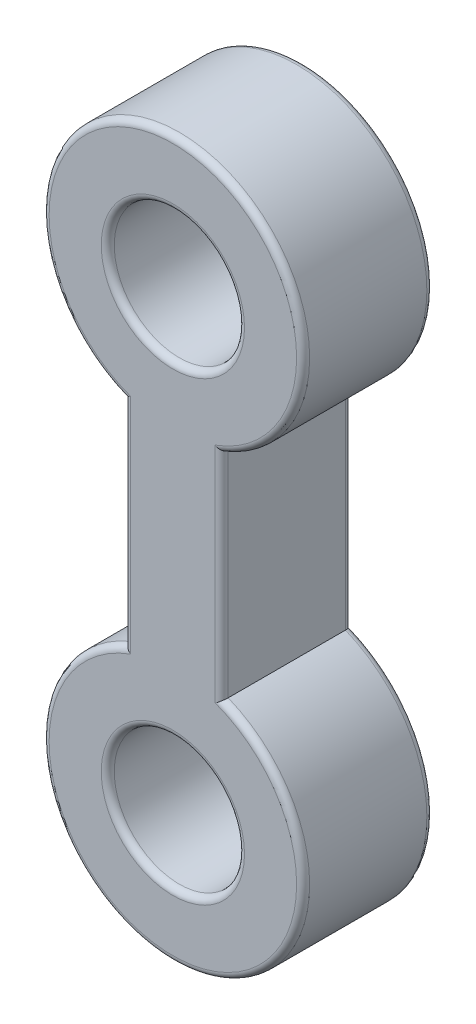
SolidWorks part; units mm, degrees
ref_plane "Front Plane" through (0, 0, 0) normal (0, 0, 1) x (1, 0, 0)
ref_plane "Top Plane" through (0, 0, 0) normal (0, 1, 0) x (1, 0, 0)
ref_plane "Right Plane" through (0, 0, 0) normal (1, 0, 0) x (0, 0, -1)
sketch "Sketch1" plane through (0, 0, 0) normal (0, 0, 1) x (1, 0, 0)
  line L0 (-7.5, -18.5405) -> (-7.5, -51.4595)
  line L1 (0, 0) -> (0, -70) construction
  line L2 (7.5, -18.5405) -> (7.5, -51.4595)
  arc A0 (7.5, -18.5405) -> (-7.5, -18.5405) centre (0, 0) ccw
  circle A1 centre (0, 0) radius 10
  arc A2 (-7.5, -51.4595) -> (7.5, -51.4595) centre (0, -70) ccw
  circle A3 centre (0, -70) radius 10
  dimension "D1" = 40
  dimension "D2" = 20
  dimension "D3" = 70
  dimension "D4" = 15
extrude "Boss-Extrude1" add sketch "Sketch1" along normal mid plane 20
fillet "Fillet1" radius 1 12 edges at (10, -70, -10) (10, 0, -10) (-7.5, -35, -10) (0, -90, -10) (7.5, -35, -10) (0, 20, -10) (10, -70, 10) (7.5, -35, 10) (0, -90, 10) (-7.5, -35, 10) (0, 20, 10) (10, 0, 10)
